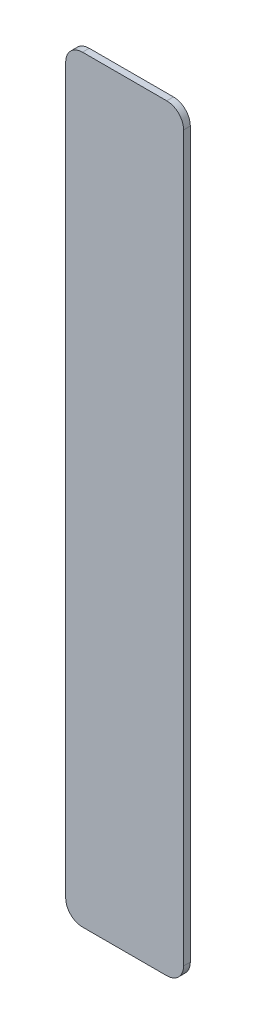
SolidWorks part; units mm, degrees
ref_plane "Front Plane" through (0, 0, 0) normal (0, 0, 1) x (1, 0, 0)
ref_plane "Top Plane" through (0, 0, 0) normal (0, 1, 0) x (1, 0, 0)
ref_plane "Right Plane" through (0, 0, 0) normal (1, 0, 0) x (0, 0, -1)
sketch "Sketch1" plane through (0, 0, 0) normal (0, 0, 1) x (1, 0, 0)
  line L1 (3.5, -22.5) -> (-3.5, -22.5)
  line L2 (3.5, -22.5) -> (3.5, 22.5)
  line L3 (3.5, 22.5) -> (-3.5, 22.5)
  line L4 (-3.5, -22.5) -> (-3.5, 22.5)
  line L5 (3.5, -22.5) -> (-3.5, 22.5) construction
  line L6 (3.5, 22.5) -> (-3.5, -22.5) construction
  point P0 (0, 0)
  dimension "D1" = 45
  dimension "D2" = 7
extrude "Boss-Extrude1" add sketch "Sketch1" along normal blind 0.4
fillet "Fillet1" radius 1 4 edges at (-3.5, -22.5, 0.2) (3.5, -22.5, 0.2) (-3.5, 22.5, 0.2) (3.5, 22.5, 0.2)
